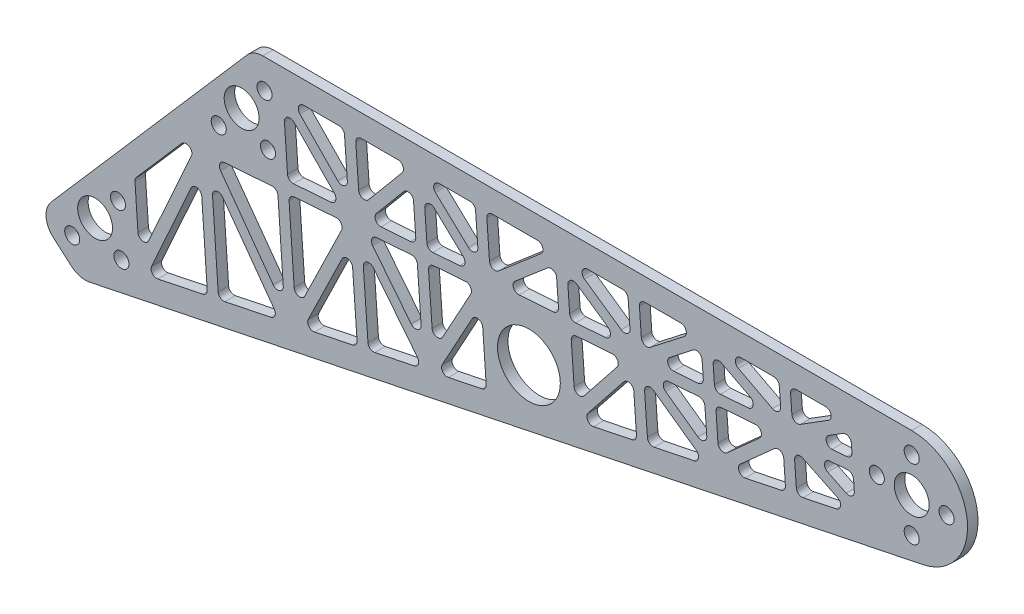
SolidWorks part; units mm, degrees
material "6061-T6 (SS)"
ref_plane "Front Plane" through (0, 0, 0) normal (0, 0, 1) x (1, 0, 0)
ref_plane "Top Plane" through (0, 0, 0) normal (0, 1, 0) x (1, 0, 0)
ref_plane "Right Plane" through (0, 0, 0) normal (1, 0, 0) x (0, 0, -1)
sketch "Sketch1" plane through (0, 0, 0) normal (0, 0, 1) x (1, 0, 0)
  line L0 (0, 0) -> (-66.6556, -76.6785) construction
  line L1 (55, 0) -> (-55, 0) construction
  line L2 (304.8, 25.4) -> (9.593, 25.4)
  line L3 (-86.6553, -80.3276) -> (2.4044, 22.124)
  line L4 (-69.2153, -103.1424) -> (309.935, -24.8755)
  line L5 (0, 15.875) -> (0, -15.875) construction
  line L6 (-15.875, 0) -> (15.875, 0) construction
  line L7 (-66.6556, -76.6785) -> (-56.2407, -64.6975) construction
  line L8 (-66.6556, -76.6785) -> (-54.6746, -87.0934) construction
  line L9 (-85.7157, -93.7651) -> (-77.3898, -101.0027)
  line L10 (304.8, 0) -> (304.8, 15.875) construction
  line L11 (0, 0) -> (-10.4149, -11.981) construction
  line L12 (0, 0) -> (11.981, -10.4149) construction
  circle A0 centre (304.8, 0) radius 7.9375
  circle A1 centre (0, 0) radius 7.9375
  circle A2 centre (-66.6556, -76.6785) radius 7.9375
  arc A7 (304.8, 25.4) -> (309.935, -24.8755) centre (304.8, 0) cw
  arc A8 (-69.2153, -103.1424) -> (-77.3898, -101.0027) centre (-71.1409, -93.8141) cw
  arc A17 (-85.7157, -93.7651) -> (-86.6553, -80.3276) centre (-79.4667, -86.5765) cw
  arc A18 (9.593, 25.4) -> (2.4044, 22.124) centre (9.593, 15.875) ccw
  circle A19 centre (304.8, 0) radius 15.875 construction
  circle A20 centre (304.8, 15.875) radius 3.429
  circle A21 centre (320.675, 0) radius 3.429
  circle A22 centre (304.8, -15.875) radius 3.429
  circle A23 centre (288.925, 0) radius 3.429
  circle A24 centre (-66.6556, -76.6785) radius 15.875 construction
  circle A25 centre (-56.2407, -64.6975) radius 3.429
  circle A26 centre (-54.6746, -87.0934) radius 3.429
  circle A27 centre (-77.0705, -88.6595) radius 3.429
  circle A28 centre (0, 0) radius 15.875 construction
  circle A29 centre (-10.4149, -11.981) radius 3.429
  circle A30 centre (11.981, -10.4149) radius 3.429
  circle A31 centre (10.4149, 11.981) radius 3.429
  circle A32 centre (130.6713, -35.9449) radius 14.2875
  point P21 (0, 0)
  point P26 (0, 0)
  dimension "D2" = 15.875
  dimension "D5" = 101.6
  dimension "D6" = 25.4
  dimension "D8" = 6.858
  dimension "D15" = 9.525
  dimension "D16" = 31.75
  dimension "D17" = 4
  dimension "D10" = 31.75
  dimension "D11" = 3
  dimension "D20" = 31.75
  dimension "D21" = 3
  dimension "D24" = 25.4
  dimension "D26" = 28.575
  dimension "D3" = 304.8
  dimension "D4" = 131
  dimension "D7" = 31.75
  dimension "D9" = 31.75
  dimension "D12" = 25.4
  dimension "D13" = 12.7
  dimension "D14" = 25.4
  dimension "D18" = 90
  dimension "D19" = 15.875
  dimension "D22" = 90
  dimension "D23" = 15.875
  dimension "D25" = 177.8
extrude "Boss-Extrude1" add sketch "Sketch1" along normal blind 4.7625
sketch "Sketch2" plane through (0, 0, 4.7625) normal (0, 0, 1) x (1, 0, 0)
  line L0 (-17.0231, -23.4827) -> (-12.9898, -81.1617) construction
  line L1 (-46.0819, -87.9928) -> (-17.0231, -23.4827) construction
  line L2 (-17.0231, -23.4827) -> (19.8909, -74.3743) construction
  line L3 (-48.3978, -86.9496) -> (-19.339, -22.4395)
  line L4 (-9.8214, -20.4693) -> (12.5746, -18.9032)
  line L5 (24.9108, -73.338) -> (18.7168, 15.24)
  line L6 (-48.5965, -52.0323) -> (-46.0819, -87.9928)
  line L7 (282.9082, -6.0168) -> (298.7832, -21.8918)
  line L8 (9.8824, 15.24) -> (-78.5709, -86.5139)
  line L9 (-78.5709, -86.5139) -> (-70.9615, -93.1287)
  line L10 (-70.9615, -93.1287) -> (307.881, -14.9253)
  line L11 (304.8, 15.24) -> (9.8824, 15.24)
  line L12 (9.8824, 15.24) -> (-78.5709, -86.5139)
  line L13 (-78.5709, -86.5139) -> (-70.9615, -93.1287)
  line L14 (-70.9615, -93.1287) -> (307.881, -14.9253)
  line L15 (304.8, 15.24) -> (9.8824, 15.24)
  line L16 (282.9082, 6.0168) -> (298.7832, 21.8918)
  line L17 (304.8, 0) -> (-38.6101, -25.0578) construction
  line L18 (304.6152, 2.5333) -> (-38.7949, -22.5246)
  line L19 (304.9848, -2.5333) -> (-38.4253, -27.5911)
  line L20 (304.8, 0) -> (-38.6101, -25.0578) construction
  line L21 (-14.4893, -23.3055) -> (-10.456, -80.9845)
  line L22 (19.8909, -74.3743) -> (13.6492, 14.8856)
  line L23 (19.8432, -73.6924) -> (13.6492, 14.8856) construction
  line L24 (2.4044, 22.124) -> (-86.6553, -80.3276) construction
  line L25 (-14.967, -21.9913) -> (21.9469, -72.8829)
  line L26 (-43.766, -89.036) -> (-14.7072, -24.5259)
  line L27 (-19.5569, -23.6599) -> (-15.4997, -81.6799)
  line L28 (-19.0792, -24.974) -> (17.8348, -75.8656)
  line L29 (51.6287, -18.4733) -> (55.1762, -67.0904) construction
  line L30 (110.9351, -14.1459) -> (113.9136, -54.9654) construction
  line L31 (82.1087, -16.2493) -> (85.3638, -60.8589) construction
  line L32 (24.9108, -73.338) -> (51.6287, -18.4733) construction
  line L33 (51.6287, -18.4733) -> (85.3638, -60.8589) construction
  line L34 (85.3638, -60.8589) -> (110.9351, -14.1459) construction
  line L35 (22.6272, -72.226) -> (49.3451, -17.3612)
  line L36 (54.162, -18.2885) -> (57.7095, -66.9056)
  line L37 (53.6161, -16.8915) -> (87.3511, -59.2771)
  line L38 (84.642, -16.0644) -> (87.897, -60.674)
  line L39 (83.1358, -59.6393) -> (109.371, -11.7132)
  line L40 (113.2835, -11.4278) -> (116.4468, -54.7806)
  line L41 (27.1944, -74.4501) -> (53.9123, -19.5854)
  line L42 (49.0955, -18.6582) -> (52.6672, -67.6083)
  line L43 (49.6414, -20.0551) -> (83.3764, -62.4407)
  line L44 (79.5755, -16.4341) -> (82.8305, -61.0437)
  line L45 (87.5918, -62.0785) -> (109.0284, -22.9186)
  line L46 (109.0284, -22.9186) -> (111.4046, -55.4834)
  line L47 (83.1358, -59.6393) -> (112.8417, -5.3731) construction
  line L48 (112.8417, -5.3731) -> (116.4468, -54.7806) construction
  line L49 (51.6287, -18.4733) -> (49.1687, 15.24) construction
  line L50 (82.1087, -16.2493) -> (79.811, 15.24) construction
  line L51 (110.9351, -14.1459) -> (108.7908, 15.24) construction
  line L52 (109.0284, -22.9186) -> (111.3803, -55.1503) construction
  line L53 (49.0955, -18.6582) -> (52.6429, -67.2753) construction
  line L54 (-19.5569, -23.6599) -> (-15.5236, -81.3389) construction
  line L55 (18.7168, 15.24) -> (51.6287, -18.4733) construction
  line L56 (51.6287, -18.4733) -> (79.811, 15.24) construction
  line L57 (79.811, 15.24) -> (110.9351, -14.1459) construction
  line L58 (81.5548, 17.0869) -> (107.9261, -7.8117)
  line L59 (107.9261, -7.8117) -> (106.2441, 15.24)
  line L60 (79.5755, -16.4341) -> (77.2778, 15.0552)
  line L61 (49.6799, -16.8442) -> (77.8622, 16.8691)
  line L62 (49.0955, -18.6582) -> (46.622, 15.24)
  line L63 (20.5343, 17.0143) -> (53.4462, -16.699)
  line L64 (78.0673, 13.3931) -> (113.944, -20.48)
  line L65 (113.944, -20.48) -> (111.3241, 15.4248)
  line L66 (84.642, -16.0644) -> (82.3443, 15.4248)
  line L67 (53.5775, -20.1024) -> (81.7598, 13.6109)
  line L68 (54.162, -18.2885) -> (51.702, 15.4248)
  line L69 (16.8993, 13.4657) -> (49.8112, -20.2476)
  line L70 (49.0955, -18.6582) -> (46.6355, 15.0552) construction
  line L71 (107.9261, -7.8117) -> (106.2576, 15.0552) construction
  line L72 (152.1752, -47.0672) -> (149.5674, -11.327)
  line L73 (149.5674, -11.327) -> (147.6288, 15.24)
  line L74 (179.9665, -9.1088) -> (182.2828, -40.8522) construction
  line L75 (212.899, -6.7058) -> (214.8993, -34.1193) construction
  line L76 (250.0247, -26.8684) -> (248.3647, -4.118) construction
  line L77 (179.9665, -9.1088) -> (178.1899, 15.24) construction
  line L78 (212.899, -6.7058) -> (211.2976, 15.24) construction
  line L79 (248.3647, -4.118) -> (246.9522, 15.24) construction
  line L80 (147.1087, -47.4369) -> (144.5008, -11.6967)
  line L81 (144.5008, -11.6967) -> (142.5623, 14.8703)
  line L82 (149.642, -47.252) -> (147.0341, -11.5118) construction
  line L83 (147.0341, -11.5118) -> (145.0956, 15.0552) construction
  line L84 (110.9351, -14.1459) -> (145.0956, 15.0552) construction
  line L85 (145.0956, 15.0552) -> (179.9665, -9.1088) construction
  line L86 (179.9665, -9.1088) -> (211.2976, 15.24) construction
  line L87 (211.2976, 15.24) -> (248.3647, -4.118) construction
  line L88 (281.8742, -20.2938) -> (280.5226, -1.7715) construction
  line L89 (280.5226, -1.7715) -> (279.2814, 15.24) construction
  line L90 (248.3647, -4.118) -> (279.2814, 15.24) construction
  line L91 (149.642, -47.252) -> (179.9665, -9.1088) construction
  line L92 (179.9665, -9.1088) -> (214.8993, -34.1193) construction
  line L93 (214.8993, -34.1193) -> (248.3647, -4.118) construction
  line L94 (248.3647, -4.118) -> (281.8742, -20.2938) construction
  line L95 (112.5855, -16.0766) -> (145.2579, 11.8524)
  line L96 (145.2579, 11.8524) -> (178.5198, -11.1965)
  line L97 (182.4998, -8.924) -> (180.7231, 15.4248)
  line L98 (151.6302, -48.8327) -> (181.9548, -10.6895)
  line L99 (177.4333, -9.2936) -> (179.7738, -41.3701)
  line L100 (178.4879, -11.174) -> (213.4206, -36.1845)
  line L101 (181.5251, -11.1144) -> (212.8563, 13.2344)
  line L102 (215.4322, -6.521) -> (217.4325, -33.9344)
  line L103 (215.4322, -6.521) -> (213.8309, 15.4248)
  line L104 (210.1218, 12.9885) -> (247.1889, -6.3694)
  line L105 (216.5948, -36.0105) -> (250.0602, -6.0092)
  line L106 (252.558, -26.6836) -> (250.898, -3.9331)
  line L107 (243.1185, -4.4059) -> (284.7272, -24.4915)
  line L108 (284.7272, -24.4915) -> (283.0559, -1.5866)
  line L109 (283.0559, -1.5866) -> (281.5077, 19.6308)
  line L110 (243.1185, -4.4059) -> (281.5077, 19.6308)
  line L111 (250.898, -3.9331) -> (249.4854, 15.4248)
  line L112 (109.2846, -12.2151) -> (144.9332, 18.2579)
  line L113 (144.9332, 18.2579) -> (181.4132, -7.0211)
  line L114 (177.4333, -9.2936) -> (175.6431, 15.24)
  line L115 (147.6537, -45.6714) -> (177.9783, -7.5281)
  line L116 (182.4998, -8.924) -> (184.816, -40.6673)
  line L117 (181.4452, -7.0436) -> (216.3779, -32.054)
  line L118 (178.4079, -7.1032) -> (209.739, 17.2456)
  line L119 (210.3657, -6.8906) -> (212.366, -34.3041)
  line L120 (210.3657, -6.8906) -> (208.7644, 15.0552)
  line L121 (212.4735, 17.4915) -> (249.5405, -1.8665)
  line L122 (213.2038, -32.228) -> (246.6692, -2.2267)
  line L123 (247.5158, -27.3863) -> (245.8314, -4.3028)
  line L124 (253.6109, -3.83) -> (279.0211, -16.0961)
  line L125 (279.0211, -16.0961) -> (277.9894, -1.9563)
  line L126 (277.9894, -1.9563) -> (277.055, 10.8492)
  line L127 (253.6109, -3.83) -> (277.055, 10.8492)
  line L128 (245.8314, -4.3028) -> (244.4054, 15.24)
  line L129 (177.4333, -9.2936) -> (179.7495, -41.037) construction
  line L130 (247.4915, -27.0533) -> (245.8314, -4.3028) construction
  line L131 (245.8314, -4.3028) -> (244.4189, 15.0552) construction
  line L132 (177.4333, -9.2936) -> (175.6566, 15.0552) construction
  circle A6 centre (130.6713, -35.9449) radius 20.6375
  circle A7 centre (130.6713, -35.9449) radius 20.6375
  arc A11 (307.881, -14.9253) -> (304.8, 15.24) centre (304.8, 0) ccw
  arc A15 (307.881, -14.9253) -> (304.8, 15.24) centre (304.8, 0) ccw
  circle A17 centre (-10.4149, -11.981) radius 8.509
  circle A18 centre (-10.4149, -11.981) radius 8.509
  circle A20 centre (11.981, -10.4149) radius 8.509
  circle A21 centre (11.981, -10.4149) radius 8.509
  circle A23 centre (10.4149, 11.981) radius 8.509
  circle A24 centre (10.4149, 11.981) radius 8.509
  circle A26 centre (-56.2407, -64.6975) radius 8.509
  circle A27 centre (-56.2407, -64.6975) radius 8.509
  circle A29 centre (-54.6746, -87.0934) radius 8.509
  circle A30 centre (-54.6746, -87.0934) radius 8.509
  circle A32 centre (304.8, -15.875) radius 8.509
  circle A33 centre (304.8, -15.875) radius 8.509
  circle A35 centre (288.925, 0) radius 8.509
  circle A36 centre (288.925, 0) radius 8.509
  circle A38 centre (304.8, 15.875) radius 8.509
  circle A39 centre (304.8, 15.875) radius 8.509
  point P213 (-38.4797, -23.3454)
  dimension "D26" = 5.08
  dimension "D28" = 2.54
  dimension "D3" = 5.08
  dimension "D4" = 5.08
  dimension "D11" = 2.54
  dimension "D14" = 33.274
  dimension "D15" = 2.54
  dimension "D17" = 30.48
  dimension "D18" = 30.48
  dimension "D19" = 2.54
  dimension "D21" = 2.54
  dimension "D23" = 30.48
  dimension "D24" = 33.02
  dimension "D25" = 35.56
  dimension "D1" = 10.16
  dimension "D2" = 6.35
  dimension "D5" = 5.08
  dimension "D6" = 5.08
  dimension "D7" = 5.08
  dimension "D8" = 5.08
  dimension "D9" = 5.08
  dimension "D10" = 5.08
  dimension "D12" = 2.54
  dimension "D13" = 5.08
  dimension "D16" = 2.54
  dimension "D20" = 2.54
  dimension "D22" = 2.54
  dimension "D27" = 2.54
  dimension "D29" = 2.54
extrude "Cut-Extrude2" cut sketch "Sketch2" against normal through all contours L3 L19 L12 L6 | L27 L26 L14 | L28 L21 L14 | L19 L25 L22 | L42 L41 L14 | L5 L35 L19 | L69 L5 L18 | L15 L63 L62 | L68 L61 L15 | L67 L18 L60 | L66 L18 L64 | L58 L59 L15 | L38 L39 L19 | L44 L19 L37 | L43 L36 L14 | L46 L45 L14 | L65 L112 L15 | L95 L18 L81 | L72 L115 L19 | L96 L73 L18 | L113 L114 L15 | L18 L120 L101 | L119 L19 L117 | L100 L116 L14 | L99 L98 L14 | L102 L122 L19 | L14 L123 L105 | L104 L103 L18 | L121 L128 L15 | L111 L110 L15 | L107 L106 L14 | L124 L125 L19 | L127 L18 L126 | L97 L118 L15
fillet "Fillet1" radius 2.54 103 edges at (274.4951, 15.24, 2.3813) (250.5911, 0.2729, 2.3813) (249.4989, 15.24, 2.3813) (252.5337, -26.3505, 2.3813) (251.2177, -8.3156, 2.3813) (277.7815, -21.1387, 2.3813) (277.8045, 0.577, 2.3813) (258.3862, -0.84, 2.3813) (277.055, 10.8492, 2.3813) (215.2474, -3.9877, 2.3813) (214.1627, 10.8783, 2.3813) (239.2716, -2.2347, 2.3813) (149.3825, -8.7937, 2.3813) (148.0154, 9.9416, 2.3813) (172.6068, -7.0991, 2.3813) (174.3724, -12.0637, 2.3813) (151.7018, -40.5795, 2.3813) (149.7522, -13.8602, 2.3813) (144.316, -9.1634, 2.3813) (118.4663, -11.0496, 2.3813) (142.9278, 9.8606, 2.3813) (153.2024, -46.8552, 2.3813) (177.9067, -15.7813, 2.3813) (179.7738, -41.3701, 2.3813) (184.7917, -40.3343, 2.3813) (182.8942, -14.3288, 2.3813) (211.5125, -34.8184, 2.3813) (187.1543, -11.1311, 2.3813) (210.5506, -9.4239, 2.3813) (211.9716, -28.8993, 2.3813) (209.1097, 10.3228, 2.3813) (210.1809, -4.3574, 2.3813) (188.1514, -5.9648, 2.3813) (47.4136, -21.3276, 2.3813) (24.5561, -68.265, 2.3813) (21.4066, -23.2253, 2.3813) (21.0522, -18.1577, 2.3813) (18.9907, 11.3234, 2.3813) (45.9942, -16.3377, 2.3813) (76.5004, 15.24, 2.3813) (53.7052, -12.0289, 2.3813) (51.7155, 15.24, 2.3813) (-43.0105, -87.3588, 2.3813) (-18.8528, -33.729, 2.3813) (-15.4997, -81.6799, 2.3813) (-10.4798, -80.6436, 2.3813) (-13.8704, -32.155, 2.3813) (17.1617, -74.9377, 2.3813) (28.0517, -72.6897, 2.3813) (49.782, -28.067, 2.3813) (52.6672, -67.6083, 2.3813) (141.4027, 15.24, 2.3813) (113.1028, -8.9513, 2.3813) (111.3376, 15.24, 2.3813) (88.6283, -60.185, 2.3813) (109.0284, -22.9186, 2.3813) (111.4046, -55.4834, 2.3813) (56.6126, -20.6564, 2.3813) (79.7603, -18.9674, 2.3813) (82.2323, -52.8457, 2.3813) (57.6852, -66.5725, 2.3813) (54.7602, -26.4865, 2.3813) (82.5756, -61.4345, 2.3813) (79.3906, -13.9008, 2.3813) (57.4216, -15.5039, 2.3813) (77.7345, 8.7956, 2.3813) (104.9967, -12.0324, 2.3813) (84.4571, -13.5311, 2.3813) (82.82, 8.9059, 2.3813) (207.1583, 15.24, 2.3813) (182.1545, -4.1916, 2.3813) (180.7366, 15.24, 2.3813) (-46.4563, -82.6395, 2.3813) (-48.5965, -52.0323, 2.3813) (-26.6, -26.7282, 2.3813) (-21.0897, -26.3262, 2.3813) (84.8268, -18.5977, 2.3813) (106.4668, -17.0187, 2.3813) (87.2704, -52.0862, 2.3813) (83.5109, 15.24, 2.3813) (106.2441, 15.24, 2.3813) (107.9261, -7.8117, 2.3813) (16.34, -23.595, 2.3813) (19.5561, -69.5868, 2.3813) (-12.2886, -25.684, 2.3813) (46.622, 15.24, 2.3813) (48.5895, -11.724, 2.3813) (149.2883, 15.24, 2.3813) (175.6431, 15.24, 2.3813) (177.0467, -3.9952, 2.3813) (219.8427, -33.0988, 2.3813) (246.2079, -9.4627, 2.3813) (247.5158, -27.3863, 2.3813) (215.6171, -9.0542, 2.3813) (241.1299, -7.1926, 2.3813) (217.056, -28.7745, 2.3813) (216.7846, 15.24, 2.3813) (244.4054, 15.24, 2.3813) (245.4997, 0.2438, 2.3813) (258.0233, -5.9599, 2.3813) (278.1742, -4.4896, 2.3813) (279.0211, -16.0961, 2.3813) (22.2665, 15.24, 2.3813)
